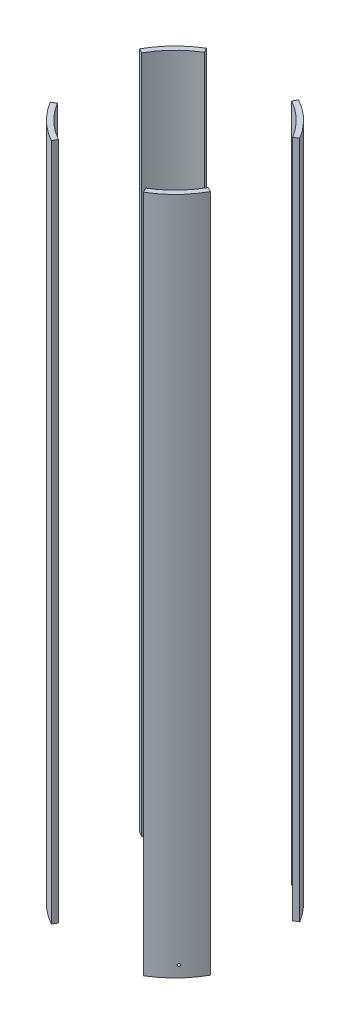
SolidWorks part; units mm, degrees
material "6061-T6 (SS)"
ref_plane "Front Plane" through (0, 0, 0) normal (0, 0, 1) x (1, 0, 0)
ref_plane "Top Plane" through (0, 0, 0) normal (0, 1, 0) x (1, 0, 0)
ref_plane "Right Plane" through (0, 0, 0) normal (1, 0, 0) x (0, 0, -1)
sketch "Sketch2" plane through (0, 0, 0) normal (0, 1, 0) x (1, 0, 0)
  circle A0 centre (0, 0) radius 88.9
  circle A1 centre (0, 0) radius 83.82
  dimension "D1" = 177.8
  dimension "D2" = 167.64
extrude "Boss-Extrude1" add sketch "Sketch2" along normal mid plane 663.4604
sketch "Sketch3" plane through (0, 0, 0) normal (0, 1, 0) x (1, 0, 0)
  line L0 (0, 0) -> (169.6618, 101.6776)
  line L1 (-58.1167, 96.9749) -> (0, 0)
  line L2 (0, 0) -> (53.9, 96.9749)
  line L3 (53.9, 96.9749) -> (-58.1167, 96.9749)
  line L4 (0, 0) -> (70.9917, -118.4586)
  line L5 (70.9917, -118.4586) -> (-65.8409, -118.4586)
  line L6 (-65.8409, -118.4586) -> (0, 0)
  line L7 (169.6618, 101.6776) -> (169.6618, -94.3004)
  line L8 (169.6618, -94.3004) -> (0, 0)
  line L9 (0, 0) -> (-123.7413, 68.7771)
  line L10 (-123.7413, 68.7771) -> (-123.7413, -74.1577)
  line L11 (-123.7413, -74.1577) -> (0, 0)
  dimension "D1" = 60
  dimension "D2" = 60
  dimension "D3" = 60
  dimension "D4" = 60
  dimension "D5" = 30
  dimension "D6" = 30
extrude "Cut-Extrude1" cut sketch "Sketch3" against normal through all both and the other way through all contours L8 L7 L0 | L2 L3 L1 | L10 L11 L9 | L6 L5 L4
ref_plane "Bolt reference plane" through (-56.3092, 0, 58.1758) normal (0.6955, 0, -0.7185) x (-0.7185, 0, -0.6955)
sketch "Sketch5" plane through (-56.3092, 0, 58.1758) normal (0.6955, 0, -0.7185) x (-0.7185, 0, -0.6955)
  line L0 (-23.009, -331.7302) -> (23.009, -331.7302) construction
  line L2 (-23.009, 331.7302) -> (-23.009, -331.7302) construction
  circle A1 centre (-1.292, -320.6177) radius 1.27
  point P9 (0, 0)
  point P10 (0, 0)
  dimension "D4" = 11.1125
  dimension "D5" = 21.717
extrude "Bolt holes" cut sketch "Sketch5" against normal through all
pattern_circular "Bolt pattern" count 4 over 360 about axis through (0, 331.7302, 0) along (0, 1, 0) of "Bolt holes"
equation "\"D1@Boss-Extrude1\"=3*12"
